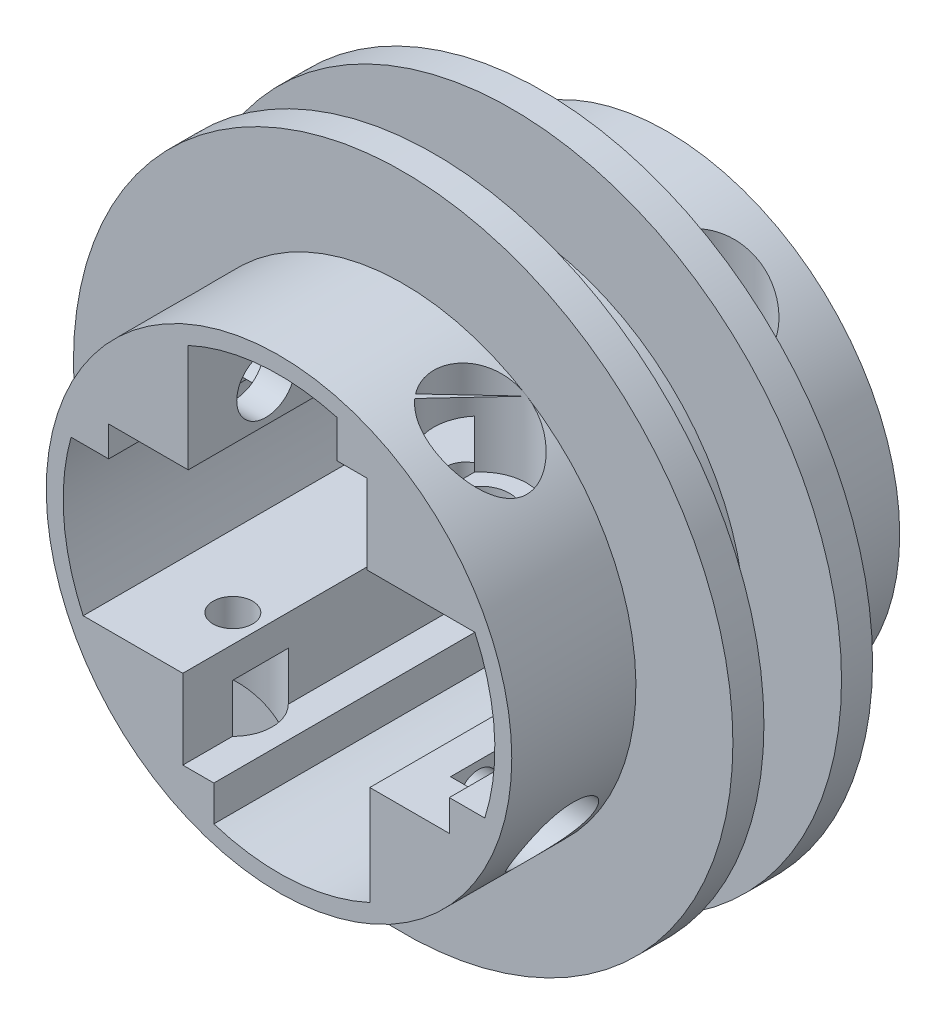
SolidWorks part; units mm, degrees
ref_plane "Front Plane" through (0, 0, 0) normal (0, 0, 1) x (1, 0, 0)
ref_plane "Top Plane" through (0, 0, 0) normal (0, 1, 0) x (1, 0, 0)
ref_plane "Right Plane" through (0, 0, 0) normal (1, 0, 0) x (0, 0, -1)
sketch "Sketch1" plane through (0, 0, 0) normal (0, 0, 1) x (1, 0, 0)
  line L0 (-11.7, 7.45) -> (-11.7, 25.24)
  line L1 (-10, -10) -> (10, -10)
  line L2 (-10, -10) -> (-10, 10)
  line L3 (-10, 10) -> (10, 10)
  line L4 (10, -10) -> (10, 10)
  line L5 (-10, -10) -> (10, 10) construction
  line L6 (-10, 10) -> (10, -10) construction
  line L7 (-11.7, 7.45) -> (-26.8038, 7.45)
  line L8 (7.45, 11.7) -> (25.24, 11.7)
  line L10 (-8.4, -11.7) -> (-25.24, -11.7)
  line L11 (11.7, -8.4) -> (11.7, -25.24)
  line L18 (11.7, -8.4) -> (26.5215, -8.4)
  line L20 (7.45, 11.7) -> (7.45, 26.8038)
  line L25 (-8.4, -11.7) -> (-8.4, -26.5215)
  circle A1 centre (0, 0) radius 27.8199
  circle A2 centre (0, 0) radius 30
  point P0 (0, 0)
  point P2 (11.7, -15.95)
  point P7 (-4.4, 10)
  point P8 (0, 10)
  point P9 (-11.7, 15.95)
  point P10 (-10, 0)
  point P13 (-11.7, 15.95)
  point P14 (10, 4.4)
  point P16 (15.95, 11.7)
  point P18 (10, 0)
  point P19 (-10, -4.4)
  point P24 (-11.7, 15.95)
  point P27 (4.4, -10)
  point P28 (0, -10)
  point P32 (-15.95, -11.7)
  point P35 (11.7, -15.95)
  point P42 (15.95, 11.7)
  point P45 (15.95, 11.7)
  point P49 (15.95, 11.7)
  point P50 (15.95, 11.7)
  point P51 (-15.95, -11.7)
  point P52 (15.95, 11.7)
  point P57 (-11.7, 7.45)
  point P58 (7.45, 11.7)
  point P59 (11.7, -8.4)
  point P60 (-8.4, -11.7)
  dimension "D16" = 4.4
  dimension "D28" = 60
  dimension "D1" = 20
  dimension "D2" = 20
  dimension "D3" = 4.4
  dimension "D4" = 7.3
  dimension "D5" = 5.95
  dimension "D6" = 17.79
  dimension "D7" = 4.4
  dimension "D8" = 7.3
  dimension "D9" = 15.1038
  dimension "D10" = 7.3
  dimension "D11" = 5.95
  dimension "D12" = 14.8215
  dimension "D13" = 16.84
  dimension "D14" = 15.1038
  dimension "D18" = 5.95
  dimension "D21" = 4.4
  dimension "D22" = 7.3
  dimension "D23" = 5.95
extrude "Boss-Extrude2" add sketch "Sketch1" along normal blind 16 contours L8 A1 L20 | L0 A1 L7 | L10 A1 L25 | L11 A1 L18 | A2 A1
sketch "Sketch2" plane through (-11.7, 0, 0) normal (1, 0, 0) x (0, 0, -1)
  line L0 (0, 15.95) -> (-16, 15.95) construction
  line L1 (-16, 7.45) -> (-16, 25.24) construction
  circle A0 centre (-8, 15.95) radius 3.6
  dimension "D1" = 7.2
extrude "Cut-Extrude1" cut sketch "Sketch2" against normal blind 16
sketch "Sketch3" plane through (0, 11.7, 0) normal (0, -1, 0) x (1, 0, 0)
  line L0 (15.95, 0) -> (15.95, 16) construction
  line L1 (7.45, 16) -> (25.24, 16) construction
  circle A0 centre (15.95, 8) radius 3.6
  dimension "D1" = 7.2
extrude "Cut-Extrude2" cut sketch "Sketch3" against normal blind 16
sketch "Sketch4" plane through (0, -11.7, 0) normal (0, 1, 0) x (1, 0, 0)
  line L0 (-15.95, 0) -> (-15.95, -16) construction
  line L1 (-8.4, -16) -> (-25.24, -16) construction
  circle A0 centre (-15.95, -8) radius 2.55
  dimension "D1" = 5.1
extrude "Cut-Extrude3" cut sketch "Sketch4" against normal blind 16
sketch "Sketch5" plane through (11.7, 0, 0) normal (-1, 0, 0) x (0, 0, 1)
  line L0 (0, -15.95) -> (16, -15.95) construction
  line L1 (16, -8.4) -> (16, -25.24) construction
  circle A0 centre (8, -15.95) radius 2.55
  dimension "D1" = 5.1
extrude "Cut-Extrude4" cut sketch "Sketch5" against normal blind 16 contours A0
ref_plane "Plane1" through (-29.7, 0, 0) normal (1, 0, 0) x (0, 0, -1)
sketch "Sketch6" plane through (-29.7, 0, 0) normal (1, 0, 0) x (0, 0, -1)
  circle A0 centre (-8, 15.95) radius 6
  point P0 (-8, 15.95)
  dimension "D1" = 12
extrude "Cut-Extrude5" cut sketch "Sketch6" along normal blind 10.75
ref_plane "Plane2" through (0, 29.7, 0) normal (0, -1, 0) x (-1, 0, 0)
sketch "Sketch8" plane through (0, 29.7, 0) normal (0, -1, 0) x (-1, 0, 0)
  circle A0 centre (-15.95, -8) radius 6
  dimension "D1" = 12
extrude "Cut-Extrude6" cut sketch "Sketch8" along normal blind 10.75
ref_plane "Plane3" through (29.7, 0, 0) normal (-1, 0, 0) x (0, 0, 1)
sketch "Sketch9" plane through (29.7, 0, 0) normal (-1, 0, 0) x (0, 0, 1)
  circle A0 centre (8, -15.95) radius 5.05
  dimension "D1" = 10.1
extrude "Cut-Extrude7" cut sketch "Sketch9" along normal blind 9.78
ref_plane "Plane4" through (0, -29.7, 0) normal (0, 1, 0) x (1, 0, 0)
sketch "Sketch10" plane through (0, -29.7, 0) normal (0, 1, 0) x (1, 0, 0)
  circle A0 centre (-15.95, -8) radius 5.05
  dimension "D1" = 10.1
extrude "Cut-Extrude9" cut sketch "Sketch10" along normal blind 9.78
sketch "Sketch11" plane through (0, 11.7, 0) normal (0, -1, 0) x (1, 0, 0)
  circle A0 centre (15.95, 8) radius 3.6 construction
  point P0 (19.55, 8)
sketch "Sketch12" plane through (0, 0, 16) normal (0, 0, 1) x (1, 0, 0)
  line L0 (7.45, 11.7) -> (7.45, 26.8038) construction
  line L1 (7.45, 11.7) -> (25.24, 11.7) construction
  line L2 (11.7, -8.4) -> (26.5215, -8.4) construction
  line L3 (11.7, -8.4) -> (11.7, -25.24) construction
  line L4 (-8.4, -11.7) -> (-8.4, -26.5215) construction
  line L5 (-8.4, -11.7) -> (-25.24, -11.7) construction
  line L6 (-11.7, 7.45) -> (-26.8038, 7.45) construction
  line L7 (-11.7, 7.45) -> (-11.7, 25.24) construction
  line L8 (7.45, 11.7) -> (7.45, 26.8038)
  line L9 (7.45, 11.7) -> (25.24, 11.7)
  line L10 (11.7, -8.4) -> (26.5215, -8.4)
  line L11 (11.7, -8.4) -> (11.7, -25.24)
  line L12 (-8.4, -11.7) -> (-8.4, -26.5215)
  line L13 (-8.4, -11.7) -> (-25.24, -11.7)
  line L14 (-11.7, 7.45) -> (-26.8038, 7.45)
  line L15 (-11.7, 7.45) -> (-11.7, 25.24)
  circle A0 centre (0, 0) radius 27.8199 construction
  circle A1 centre (0, 0) radius 30 construction
  circle A2 centre (0, 0) radius 27.8199
  circle A3 centre (0, 0) radius 30
  line M1 (7.45, 11.7) -> (25.24, 11.7)
  arc M2 (25.24, 11.7) -> (26.5215, -8.4) centre (0, 0) cw
  line M3 (26.5215, -8.4) -> (11.7, -8.4)
  line M4 (11.7, -8.4) -> (11.7, -25.24)
  arc M5 (11.7, -25.24) -> (-8.4, -26.5215) centre (0, 0) cw
  line M6 (-8.4, -26.5215) -> (-8.4, -11.7)
  line M7 (-8.4, -11.7) -> (-25.24, -11.7)
  arc M8 (-25.24, -11.7) -> (-26.8038, 7.45) centre (0, 0) cw
  line M9 (-26.8038, 7.45) -> (-11.7, 7.45)
  line M10 (-11.7, 7.45) -> (-11.7, 25.24)
  arc M11 (-11.7, 25.24) -> (7.45, 26.8038) centre (0, 0) cw
  line M12 (7.45, 26.8038) -> (7.45, 11.7)
  circle M13 centre (0, 0) radius 30
extrude "Boss-Extrude3" add sketch "Sketch12" along normal blind 7 contours A2 M10 M9 | A2 M1 M12 | A2 M4 M3 | A2 M7 M6 | A2 M13 M2 M5 M8 M11 | L15 L14
ref_plane "Plane5" through (0, 0, 23) normal (0, 0, 1) x (1, 0, 0)
mirror "Mirror2" about plane through (0, 0, 23) normal (0, 0, 1) of bodies 110
sketch "Sketch13" plane through (0, 0, 46) normal (0, 0, 1) x (1, 0, 0)
  line L0 (7.45, 11.7) -> (7.45, 26.8038) construction
  line L1 (7.45, 11.7) -> (25.24, 11.7) construction
  line L2 (11.7, -8.4) -> (26.5215, -8.4) construction
  line L3 (11.7, -8.4) -> (11.7, -25.24) construction
  line L4 (-8.4, -11.7) -> (-8.4, -26.5215) construction
  line L5 (-8.4, -11.7) -> (-25.24, -11.7) construction
  line L6 (-11.7, 7.45) -> (-26.8038, 7.45) construction
  line L7 (-11.7, 7.45) -> (-11.7, 25.24) construction
  line L8 (7.45, 11.7) -> (7.45, 26.8038)
  line L9 (7.45, 11.7) -> (25.24, 11.7)
  line L10 (11.7, -8.4) -> (26.5215, -8.4)
  line L11 (11.7, -8.4) -> (11.7, -25.24)
  line L12 (-8.4, -11.7) -> (-8.4, -26.5215)
  line L13 (-8.4, -11.7) -> (-25.24, -11.7)
  line L14 (-11.7, 7.45) -> (-26.8038, 7.45)
  line L15 (-11.7, 7.45) -> (-11.7, 25.24)
  circle A0 centre (0, 0) radius 30 construction
  arc A1 (7.45, 26.8038) -> (-11.7, 25.24) centre (0, 0) ccw construction
  arc A2 (26.5215, -8.4) -> (25.24, 11.7) centre (0, 0) ccw construction
  arc A3 (-8.4, -26.5215) -> (11.7, -25.24) centre (0, 0) ccw construction
  arc A4 (-26.8038, 7.45) -> (-25.24, -11.7) centre (0, 0) ccw construction
  circle A5 centre (0, 0) radius 30
  arc A6 (7.45, 26.8038) -> (-11.7, 25.24) centre (0, 0) ccw
  arc A7 (26.5215, -8.4) -> (25.24, 11.7) centre (0, 0) ccw
  arc A8 (-8.4, -26.5215) -> (11.7, -25.24) centre (0, 0) ccw
  arc A9 (-26.8038, 7.45) -> (-25.24, -11.7) centre (0, 0) ccw
extrude "Boss-Extrude4" add sketch "Sketch13" along normal blind 3
sketch "Sketch14" plane through (0, 0, 49) normal (0, 0, 1) x (1, 0, 0)
  circle A0 centre (0, 0) radius 27.8199
  circle A1 centre (0, 0) radius 42.5
  dimension "D1" = 85
extrude "Boss-Extrude5" add sketch "Sketch14" against normal blind 3
sketch "Sketch15" plane through (0, 0, 0) normal (0, 0, -1) x (-1, 0, 0)
  line L0 (11.7, 7.45) -> (11.7, 25.24) construction
  line L1 (11.7, 7.45) -> (26.8038, 7.45) construction
  line L2 (8.4, -11.7) -> (25.24, -11.7) construction
  line L3 (8.4, -11.7) -> (8.4, -26.5215) construction
  line L4 (-11.7, -8.4) -> (-11.7, -25.24) construction
  line L5 (-11.7, -8.4) -> (-26.5215, -8.4) construction
  line L6 (-7.45, 11.7) -> (-25.24, 11.7) construction
  line L7 (-7.45, 11.7) -> (-7.45, 26.8038) construction
  line L8 (11.7, 7.45) -> (11.7, 25.24)
  line L9 (11.7, 7.45) -> (26.8038, 7.45)
  line L10 (8.4, -11.7) -> (25.24, -11.7)
  line L11 (8.4, -11.7) -> (8.4, -26.5215)
  line L12 (-11.7, -8.4) -> (-11.7, -25.24)
  line L13 (-11.7, -8.4) -> (-26.5215, -8.4)
  line L14 (-7.45, 11.7) -> (-25.24, 11.7)
  line L15 (-7.45, 11.7) -> (-7.45, 26.8038)
  arc A0 (-25.24, 11.7) -> (-26.5215, -8.4) centre (0, 0) ccw construction
  circle A1 centre (0, 0) radius 30 construction
  arc A2 (11.7, 25.24) -> (-7.45, 26.8038) centre (0, 0) ccw construction
  arc A3 (25.24, -11.7) -> (26.8038, 7.45) centre (0, 0) ccw construction
  arc A4 (-11.7, -25.24) -> (8.4, -26.5215) centre (0, 0) ccw construction
  arc A5 (-25.24, 11.7) -> (-26.5215, -8.4) centre (0, 0) ccw
  circle A6 centre (0, 0) radius 30
  arc A7 (11.7, 25.24) -> (-7.45, 26.8038) centre (0, 0) ccw
  arc A8 (25.24, -11.7) -> (26.8038, 7.45) centre (0, 0) ccw
  arc A9 (-11.7, -25.24) -> (8.4, -26.5215) centre (0, 0) ccw
extrude "Boss-Extrude6" add sketch "Sketch15" along normal blind 3
sketch "Sketch16" plane through (0, 0, -3) normal (0, 0, -1) x (-1, 0, 0)
  circle A0 centre (0, 0) radius 27.8199
  circle A1 centre (0, 0) radius 42.5
  dimension "D1" = 85
extrude "Boss-Extrude7" add sketch "Sketch16" against normal blind 3
sketch "Sketch17" plane through (0, 0, -3) normal (0, 0, -1) x (-1, 0, 0)
  circle A1 centre (0, 0) radius 28.5
  circle A2 centre (0, 0) radius 29.9
  dimension "D1" = 57
  dimension "D2" = 59.8
extrude "Boss-Extrude8" add sketch "Sketch17" along normal blind 17
sketch "Sketch18" plane through (0, 0, 49) normal (0, 0, 1) x (1, 0, 0)
  circle A0 centre (0, 0) radius 28.5
  circle A1 centre (0, 0) radius 29.9
  dimension "D1" = 57
  dimension "D2" = 59.8
extrude "Boss-Extrude9" add sketch "Sketch18" along normal blind 17
sketch "Sketch19" plane through (0, 0, 66) normal (0, 0, 1) x (1, 0, 0)
  line L0 (0, 8.3703) -> (0, -9.5141) construction
  line L1 (-10.9178, 0) -> (9.982, 0) construction
  circle A0 centre (0, 0) radius 5.0204
  point P5 (0, 0)
ref_plane "Plane6" through (0, 42.5, 0) normal (0, 1, 0) x (1, 0, 0)
ref_plane "Plane7" through (0, -42.5, 0) normal (0, 1, 0) x (1, 0, 0)
ref_plane "Plane8" through (42.5, 0, 0) normal (1, 0, 0) x (0, 0, -1)
ref_plane "Plane9" through (-42.5, 0, 0) normal (1, 0, 0) x (0, 0, -1)
sketch "Sketch20" plane through (0, 0, 49) normal (0, 0, 1) x (1, 0, 0)
  line L0 (12.35, 11.7) -> (19.55, 11.7) construction
  line L1 (12.35, 11.7) -> (19.55, 11.7)
  line L2 (21.95, 18.95) -> (9.95, 18.95) construction
  line L3 (21.95, 18.95) -> (9.95, 18.95)
  line L4 (-11.7, 12.35) -> (-11.7, 19.55) construction
  line L5 (-11.7, 12.35) -> (-11.7, 19.55)
  line L6 (-11.7, 12.35) -> (12.35, 12.35) construction
  line L7 (-11.7, 19.55) -> (12.35, 19.55) construction
  line L8 (-11.7, 15.95) -> (12.35, 15.95) construction
  line L9 (12.35, 15.95) -> (12.35, 18.45) construction
  line L10 (-11.7, 15.95) -> (4.72, 15.95)
  line L11 (11.35, 11.7) -> (11.35, 19.55)
  line L12 (25.24, 11.7) -> (7.45, 11.7) construction
  line L13 (11.7, -13.4) -> (11.7, -18.5) construction
  line L14 (11.7, -13.4) -> (11.7, -18.5)
  line L15 (19.92, -21) -> (19.92, -10.9) construction
  line L16 (19.92, -21) -> (19.92, -10.9)
  line L17 (15.95, 11.7) -> (15.95, -13.4) construction
  line L18 (11.35, 21.95) -> (7.45, 21.95)
  line L19 (11.35, 21.95) -> (11.35, 11.7)
  line L20 (11.35, 11.7) -> (7.45, 11.7)
  line L21 (7.45, 21.95) -> (7.45, 11.7)
  line L22 (-21, -19.92) -> (-10.9, -19.92) construction
  line L23 (21.95, -12.4) -> (11.7, -12.4)
  line L24 (21.95, -12.4) -> (21.95, -8.4)
  line L25 (21.95, -8.4) -> (11.7, -8.4)
  line L26 (11.7, -12.4) -> (11.7, -8.4)
  line L27 (-13.4, -11.7) -> (-18.5, -11.7) construction
  line L28 (-21, -19.92) -> (-10.9, -19.92)
  line L29 (-13.4, -11.7) -> (-18.5, -11.7)
  line L30 (11.7, -15.95) -> (-13.4, -15.95) construction
  line L31 (-8.4, -26.5215) -> (-8.4, -11.7) construction
  line L32 (-18.95, 21.95) -> (-18.95, 9.95) construction
  line L33 (-12.4, -21.95) -> (-8.4, -21.95)
  line L34 (-12.4, -21.95) -> (-12.4, -11.7)
  line L35 (-12.4, -11.7) -> (-8.4, -11.7)
  line L36 (-8.4, -21.95) -> (-8.4, -11.7)
  line L37 (-18.95, 21.95) -> (-18.95, 9.95)
  line L38 (-15.95, -11.7) -> (-15.95, 12.35) construction
  line L40 (-21.95, 11.35) -> (-11.7, 11.35)
  line L41 (-21.95, 11.35) -> (-21.95, 7.45)
  line L42 (-21.95, 7.45) -> (-11.7, 7.45)
  line L43 (-11.7, 11.35) -> (-11.7, 7.45)
  point P17 (11.35, 21.95)
  point P18 (11.35, 9.95)
  point P30 (21.95, -12.4)
  point P42 (-12.4, -21.95)
  point P52 (-21.95, 11.35)
  dimension "D1" = 2.5
  dimension "D2" = 16.42
  dimension "D3" = 7.63
  dimension "D4" = 1
  dimension "D5" = 6
  dimension "D6" = 6
  dimension "D7" = 1
  dimension "D8" = 6
  dimension "D9" = 1
  dimension "D10" = 5
  dimension "D11" = 6
  dimension "D12" = 4.9
  dimension "D13" = 1
  dimension "D14" = 6
extrude "Cut-Extrude10" cut sketch "Sketch20" against normal up to next
ref_plane "Plane10" through (0, 30, 0) normal (0, 1, 0) x (1, 0, 0)
sketch "Sketch21" plane through (0, 30, 0) normal (0, 1, 0) x (1, 0, 0)
  line L0 (-30, 0) -> (-30, -46) construction
  circle A0 centre (-3, -23) radius 1
  point P2 (-30, -23)
  dimension "D2" = 2
  dimension "D1" = 0
  dimension "D3" = 27
extrude "Cut-Extrude11" cut sketch "Sketch21" against normal blind 10
ref_plane "Plane11" through (0, 0, 32) normal (0, 0, -1) x (-1, 0, 0)
sketch "Sketch22" plane through (0, 0, 32) normal (0, 0, -1) x (-1, 0, 0)
  circle A0 centre (0, 0) radius 29.9
  circle A1 centre (0, 0) radius 42.5
extrude "Boss-Extrude10" add sketch "Sketch22" along normal blind 4
sketch "Sketch23" plane through (0, 0, 46) normal (0, 0, -1) x (-1, 0, 0)
  circle A0 centre (0, 0) radius 29.9
  circle A1 centre (0, 0) radius 42.5
extrude "Cut-Extrude12" cut sketch "Sketch23" against normal blind 4
ref_plane "Plane12" through (0, 0, 14) normal (0, 0, 1) x (1, 0, 0)
sketch "Sketch24" plane through (0, 0, 14) normal (0, 0, 1) x (1, 0, 0)
  circle A0 centre (0, 0) radius 30
  circle A1 centre (0, 0) radius 42.5
extrude "Boss-Extrude11" add sketch "Sketch24" along normal blind 4
sketch "Sketch26" plane through (0, 0, 0) normal (0, 0, 1) x (1, 0, 0)
  circle A0 centre (0, 0) radius 29.9
  circle A1 centre (0, 0) radius 42.5
extrude "Cut-Extrude13" cut sketch "Sketch26" against normal blind 4
sketch "Sketch27" plane through (0, 0, 66) normal (0, 0, 1) x (1, 0, 0)
  circle A0 centre (0, 0) radius 30
  circle A1 centre (0, 0) radius 29.9
extrude "Boss-Extrude13" add sketch "Sketch27" against normal blind 21
sketch "Sketch28" plane through (0, 0, -20) normal (0, 0, -1) x (-1, 0, 0)
  circle A0 centre (0, 0) radius 30
  circle A1 centre (0, 0) radius 29.9
extrude "Boss-Extrude14" add sketch "Sketch28" against normal blind 21
sketch "Sketch29" plane through (0, 0, -20) normal (0, 0, -1) x (-1, 0, 0)
  circle A0 centre (0, 0) radius 36.281
extrude "Cut-Extrude14" cut sketch "Sketch29" against normal blind 18
sketch "Sketch30" plane through (0, 0, 66) normal (0, 0, 1) x (1, 0, 0)
  circle A0 centre (0, 0) radius 33.1763
extrude "Cut-Extrude15" cut sketch "Sketch30" against normal blind 18
sketch "Sketch31" plane through (0, 30, 0) normal (0, 1, 0) x (1, 0, 0)
  circle A0 centre (4, -23) radius 1
  circle A1 centre (-3, -23) radius 1 construction
  dimension "D1" = 2
  dimension "D2" = 7
  dimension "D3" = 0
extrude "Cut-Extrude16" cut sketch "Sketch31" against normal blind 10
sketch "Sketch32" plane through (0, 0, 48) normal (0, 0, 1) x (1, 0, 0)
  line L0 (-11.7, 11.35) -> (-21.95, 11.35) construction
  line L1 (-14.95, 11.35) -> (-14.95, 23.4616)
  line L2 (-14.95, 11.35) -> (-11.7, 11.35)
  line L3 (-11.7, 11.35) -> (-11.7, 25.24)
  line L4 (11.35, 11.7) -> (11.35, 21.95) construction
  circle A0 centre (0, 0) radius 27.8199
  point P0 (-14.95, 11.35)
  point P12 (11.35, 14.91)
  dimension "D1" = 3.25
sketch "Sketch33" plane through (-18.95, 0, 0) normal (-1, 0, 0) x (0, 0, 1)
  circle A0 centre (8, 15.95) radius 3.6
  circle A1 centre (8, 15.95) radius 6
  circle A2 centre (38, 15.95) radius 3.6
  circle A3 centre (38, 15.95) radius 6
extrude "Cut-Extrude17" cut sketch "Sketch33" against normal blind 3.25
sketch "Sketch34" plane through (0, -19.92, 0) normal (0, -1, 0) x (1, 0, 0)
  circle A0 centre (-15.95, 38) radius 2.55
  circle A1 centre (-15.95, 38) radius 5.05
  circle A2 centre (-15.95, 8) radius 2.55
  circle A3 centre (-15.95, 8) radius 5.05
extrude "Cut-Extrude18" cut sketch "Sketch34" against normal blind 4.22
sketch "Sketch35" plane through (19.92, 0, 0) normal (1, 0, 0) x (0, 0, -1)
  circle A0 centre (-38, -15.95) radius 2.55
  circle A1 centre (-38, -15.95) radius 5.05
  circle A2 centre (-8, -15.95) radius 2.55
  circle A3 centre (-8, -15.95) radius 5.05
extrude "Cut-Extrude19" cut sketch "Sketch35" against normal blind 4.22
sketch "Sketch37" plane through (0, 18.95, 0) normal (0, 1, 0) x (1, 0, 0)
  circle A0 centre (15.95, -38) radius 3.6
  circle A1 centre (15.95, -38) radius 6
  circle A2 centre (15.95, -8) radius 3.6
  circle A3 centre (15.95, -8) radius 6
extrude "Cut-Extrude20" cut sketch "Sketch37" against normal blind 3.25
sketch "Sketch38" plane through (0, 15.7, 0) normal (0, 1, 0) x (1, 0, 0)
  circle A0 centre (15.95, -38) radius 3.75
  circle A1 centre (15.95, -8) radius 3.75
  dimension "D1" = 7.5
  dimension "D2" = 7.5
extrude "Cut-Extrude21" cut sketch "Sketch38" against normal blind 5
sketch "Sketch39" plane through (-15.7, 0, 0) normal (-1, 0, 0) x (0, 0, 1)
  circle A0 centre (38, 15.95) radius 3.75
  circle A1 centre (8, 15.95) radius 3.75
  dimension "D1" = 7.5
  dimension "D2" = 7.5
extrude "Cut-Extrude22" cut sketch "Sketch39" against normal blind 5
